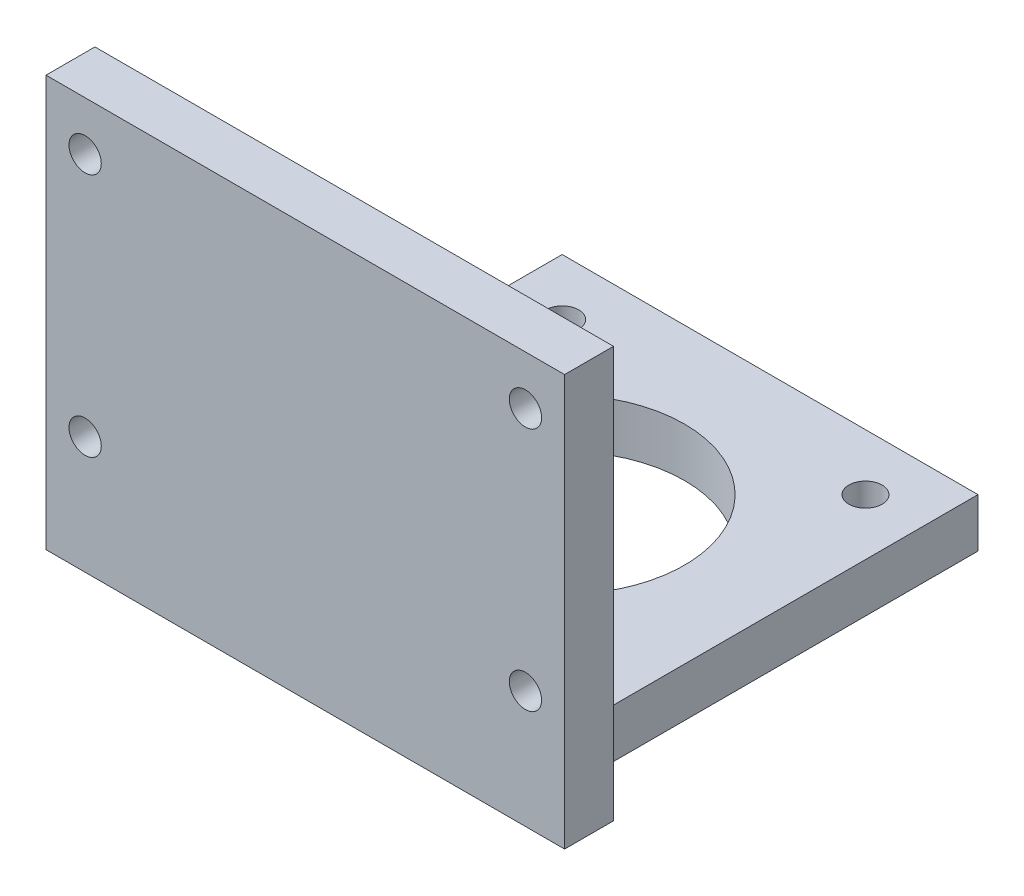
SolidWorks part; units mm, degrees
ref_plane "Front Plane" through (0, 0, 0) normal (0, 0, 1) x (1, 0, 0)
ref_plane "Top Plane" through (0, 0, 0) normal (0, 1, 0) x (1, 0, 0)
ref_plane "Right Plane" through (0, 0, 0) normal (1, 0, 0) x (0, 0, -1)
sketch "Sketch1" plane through (0, 0, 0) normal (0, 1, 0) x (1, 0, 0)
  line L1 (-21.25, 21.25) -> (21.25, 21.25)
  line L2 (-21.25, 21.25) -> (-21.25, -21.25)
  line L3 (-21.25, -21.25) -> (21.25, -21.25)
  line L4 (21.25, 21.25) -> (21.25, -21.25)
  circle A0 centre (-15.5, 15.5) radius 1.7
  circle A1 centre (15.5, 15.5) radius 1.7
  circle A2 centre (-15.5, -15.5) radius 1.7
  circle A3 centre (15.5, -15.5) radius 1.7
  circle A4 centre (0, 0) radius 12.5
  point P0 (0, 0)
  dimension "D3" = 3.4
  dimension "D4" = 3.4
  dimension "D5" = 3.4
  dimension "D6" = 3.4
  dimension "D13" = 25
  dimension "D1" = 42.5
  dimension "D2" = 42.5
  dimension "D7" = 31
  dimension "D8" = 31
  dimension "D9" = 31
  dimension "D10" = 15.5
  dimension "D11" = 15.5
  dimension "D12" = 15.5
extrude "Boss-Extrude1" add sketch "Sketch1" along normal blind 5
sketch "Sketch3" plane through (0, 0, 0) normal (0, 1, 0) x (1, 0, 0)
  line L0 (-26.5, -21.25) -> (26.5, -21.25)
  line L2 (-26.5, -21.25) -> (-26.5, -26.25)
  line L3 (-26.5, -26.25) -> (26.5, -26.25)
  line L4 (26.5, -21.25) -> (26.5, -26.25)
  line L5 (-18.0503, -21.25) -> (26.5, -26.25) construction
  line L6 (-26.5, -26.25) -> (18.0503, -21.25) construction
  point P0 (0, -23.2758)
  dimension "D1" = 53
  dimension "D2" = 26.5
  dimension "D3" = 5
extrude "Boss-Extrude3" add sketch "Sketch3" along normal blind 42
sketch "Sketch4" plane through (0, 0, 26.25) normal (0, 0, 1) x (1, 0, 0)
  line L0 (-26.5, 42) -> (26.5, 42) construction
  circle A0 centre (22.5, 37) radius 1.65
  circle A1 centre (22.5, 12) radius 1.65
  circle A2 centre (-22.5, 37) radius 1.65
  circle A3 centre (-22.5, 12) radius 1.65
  dimension "D5" = 3.3
  dimension "D6" = 3.3
  dimension "D7" = 3.3
  dimension "D8" = 3.3
  dimension "D1" = 22.5
  dimension "D2" = 22.5
  dimension "D3" = 22.5
  dimension "D4" = 22.5
  dimension "D9" = 25
  dimension "D10" = 25
  dimension "D11" = 5
  dimension "D12" = 5
extrude "Cut-Extrude1" cut sketch "Sketch4" against normal blind 42
